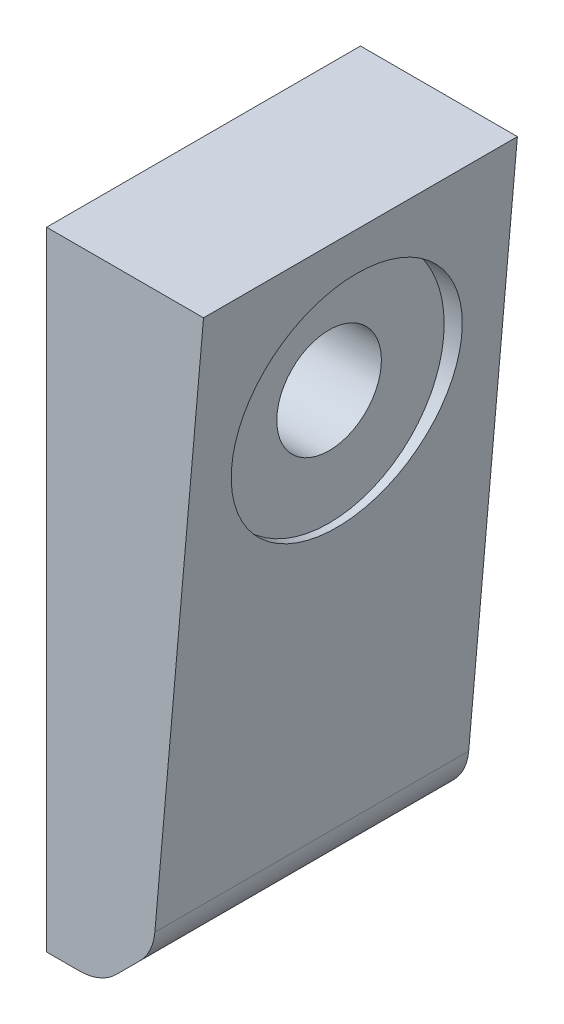
SolidWorks part; units mm, degrees
ref_plane "Спереди" through (0, 0, 0) normal (0, 0, 1) x (1, 0, 0)
ref_plane "Сверху" through (0, 0, 0) normal (0, 1, 0) x (1, 0, 0)
ref_plane "Справа" through (0, 0, 0) normal (1, 0, 0) x (0, 0, -1)
sketch "Эскиз1" plane through (0, 0, 0) normal (0, 0, 1) x (1, 0, 0)
  line L0 (0, 0) -> (0, -60)
  line L1 (0, 0) -> (15, 0)
  line L2 (0, -60) -> (3.1171, -60)
  line L3 (6.6526, -58.5355) -> (8.9013, -56.2868)
  line L4 (10.3467, -53.1871) -> (15, 0)
  arc A0 (10.3467, -53.1871) -> (8.9013, -56.2868) centre (5.3658, -52.7513) cw
  arc A1 (6.6526, -58.5355) -> (3.1171, -60) centre (3.1171, -55) cw
  point P8 (10.1881, -55)
  point P11 (5.1881, -60)
  dimension "D6" = 5
  dimension "D1" = 60
  dimension "D2" = 45
  dimension "D3" = 40
  dimension "D4" = 15
  dimension "D5" = 5
extrude "Бобышка-Вытянуть1" add sketch "Эскиз1" along normal blind 30
sketch "Эскиз3" plane through (0, 0, 0) normal (-1, 0, 0) x (0, 0, 1)
  line L0 (15, 0) -> (15, -60) construction
  line L1 (30, 0) -> (0, 0) construction
  line L2 (30, -60) -> (0, -60) construction
  circle A0 centre (15, -15) radius 5
  dimension "D1" = 10
  dimension "D2" = 15
extrude "Вырез-Вытянуть2" cut sketch "Эскиз3" against normal blind 21 contours A0
sketch "Эскиз5" plane through (0, 0, 0) normal (-1, 0, 0) x (0, 0, 1)
  line L0 (20, -15) -> (10, -15) construction
  line L1 (15, -20) -> (15, -10) construction
  circle A0 centre (15, -15) radius 5 construction
  circle A1 centre (15, -15) radius 11
  dimension "D1" = 22
extrude "Вырез-Вытянуть3" cut sketch "Эскиз5" along normal blind 3 from offset 15 contours A1
